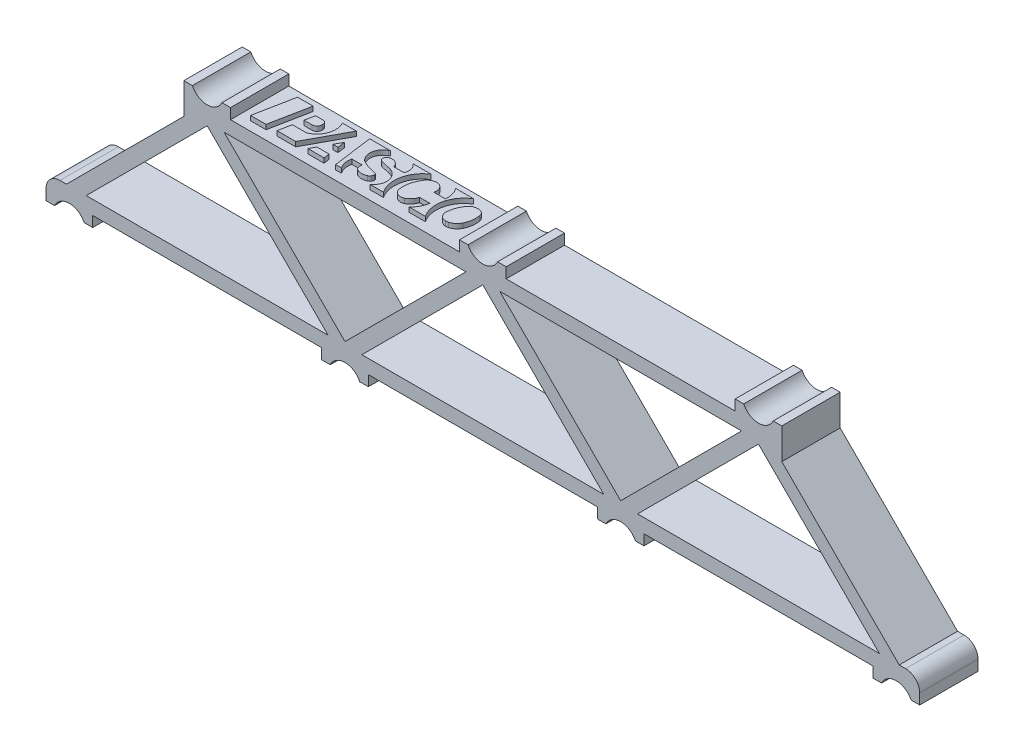
SolidWorks part; units mm, degrees
ref_plane "Front XY" through (0, 0, 0) normal (0, 0, 1) x (1, 0, 0)
ref_plane "Top XZ" through (0, 0, 0) normal (0, 1, 0) x (1, 0, 0)
ref_plane "Right YZ" through (0, 0, 0) normal (1, 0, 0) x (0, 0, -1)
sketch "Sketch1" plane through (0, 0, 0) normal (0, 0, 1) x (1, 0, 0)
  line L0 (-45, -15) -> (-15, -15) construction
  line L1 (-15, -15) -> (15, -15) construction
  line L2 (15, -15) -> (45, -15) construction
  line L3 (-45, -15) -> (-30, 0) construction
  line L4 (-30, 0) -> (-15, -15) construction
  line L5 (-15, -15) -> (0, 0) construction
  line L6 (0, 0) -> (15, -15) construction
  line L7 (15, -15) -> (30, 0) construction
  line L8 (30, 0) -> (45, -15) construction
  line L9 (-30, 0) -> (0, 0) construction
  line L10 (0, 0) -> (30, 0) construction
  line L11 (-43.1604, -14.238) -> (-30, -1.0776)
  line L12 (-30, -1.0776) -> (-16.8396, -14.238)
  line L13 (-43.1604, -14.238) -> (-16.8396, -14.238)
  line L14 (-28.1604, -0.762) -> (-15, -13.9224)
  line L15 (-15, -13.9224) -> (-1.8396, -0.762)
  line L16 (-28.1604, -0.762) -> (-1.8396, -0.762)
  line L17 (-13.1604, -14.238) -> (0, -1.0776)
  line L18 (0, -1.0776) -> (13.1604, -14.238)
  line L19 (-13.1604, -14.238) -> (13.1604, -14.238)
  line L20 (1.8396, -0.762) -> (15, -13.9224)
  line L21 (15, -13.9224) -> (28.1604, -0.762)
  line L22 (1.8396, -0.762) -> (28.1604, -0.762)
  line L23 (16.8396, -14.238) -> (30, -1.0776)
  line L24 (30, -1.0776) -> (43.1604, -14.238)
  line L25 (16.8396, -14.238) -> (43.1604, -14.238)
  line L26 (-46.8396, -15.762) -> (-30.3156, 0.762)
  line L27 (-30.3156, 0.762) -> (0, 0.762)
  line L28 (0, 0.762) -> (30.3156, 0.762)
  line L29 (30.3156, 0.762) -> (46.8396, -15.762)
  line L30 (15, -15.762) -> (46.8396, -15.762)
  line L31 (-15, -15.762) -> (15, -15.762)
  line L32 (-46.8396, -15.762) -> (-15, -15.762)
  dimension "D1" = 45
  dimension "D2" = 30
extrude "Boss-Extrude1" add sketch "Sketch1" along normal mid plane 6.35
sketch "Sketch2" plane through (0, 0, 0) normal (0, 0, 1) x (1, 0, 0)
  line L0 (-45, -15) -> (-45, -17.667) construction
  line L1 (-46.8396, -15.762) -> (-15, -15.762) construction
  line L2 (-46.6064, -16.905) -> (-47.54, -16.905)
  line L3 (-47.54, -16.905) -> (-47.54, -14.238)
  line L4 (-43.3936, -16.905) -> (-42.46, -16.905)
  line L5 (-42.46, -16.905) -> (-42.46, -14.238)
  line L6 (-42.46, -14.238) -> (-47.54, -14.238)
  line L7 (-27.46, 0.762) -> (-30.3156, 0.762)
  line L8 (-15, -15) -> (-15, -17.667) construction
  line L9 (-16.6064, -16.905) -> (-17.54, -16.905)
  line L10 (-17.54, -16.905) -> (-17.54, -15.762)
  line L11 (-13.3936, -16.905) -> (-12.46, -16.905)
  line L12 (-12.46, -16.905) -> (-12.46, -15.762)
  line L13 (-12.46, -15.762) -> (-17.54, -15.762)
  line L14 (-30.3156, 0.762) -> (0, 0.762) construction
  line L15 (-30, 0) -> (-30, 2.667) construction
  line L16 (-27.46, 0.762) -> (-27.46, 1.905)
  line L17 (-27.46, 1.905) -> (-28.3936, 1.905)
  line L18 (-32.54, 0.762) -> (-32.54, 1.905)
  line L19 (-32.54, 1.905) -> (-31.6064, 1.905)
  line L20 (-30.3156, 0.762) -> (-32.54, -1.4624)
  line L21 (-46.8396, -15.762) -> (-30.3156, 0.762) construction
  line L22 (-32.54, -1.4624) -> (-32.54, 0.762)
  line L23 (-46.8396, -15.762) -> (46.8396, -15.762) construction
  line L24 (-43.1604, -14.238) -> (-16.8396, -14.238) construction
  arc A0 (-43.3936, -16.905) -> (-46.6064, -16.905) centre (-45, -17.667) ccw
  arc A1 (-13.3936, -16.905) -> (-16.6064, -16.905) centre (-15, -17.667) ccw
  arc A2 (-31.6064, 1.905) -> (-28.3936, 1.905) centre (-30, 2.667) ccw
  dimension "D1" = 1.778
  dimension "D4" = 1.778
  dimension "D9" = 5.08
  dimension "D2" = 1.905
  dimension "D3" = 1.143
  dimension "D5" = 5.08
  dimension "D6" = 1.143
  dimension "D7" = 5.08
  dimension "D8" = 1.143
extrude "Boss-Extrude2" add sketch "Sketch2" against normal up to surface (3.175 mm away) and the other way up to surface (3.175 mm away) up to face at (15, -5.1488, -3.175) other way up to face at (15, -5.1488, 3.175)
sketch "Sketch3" plane through (0, 0, 0) normal (0, 0, 1) x (1, 0, 0)
  line L0 (0, 0) -> (0, 2.667) construction
  line L1 (1.6064, 1.905) -> (2.54, 1.905)
  line L2 (2.54, 1.905) -> (2.54, 0.762)
  line L3 (0, 0.762) -> (30.3156, 0.762) construction
  line L4 (2.54, 0.762) -> (-2.54, 0.762)
  line L5 (-30.3156, 0.762) -> (0, 0.762) construction
  line L6 (-2.54, 1.905) -> (-2.54, 0.762)
  line L7 (-1.6064, 1.905) -> (-2.54, 1.905)
  line L9 (-12.46, -15.762) -> (-17.54, -15.762) construction
  line L10 (-45, -15) -> (-45, -17.667) construction
  arc A0 (-1.6064, 1.905) -> (1.6064, 1.905) centre (0, 2.667) ccw
  arc A1 (-43.3936, -16.905) -> (-46.6064, -16.905) centre (-45, -17.667) ccw construction
  dimension "D1" = 1.143
extrude "Boss-Extrude3" add sketch "Sketch3" against normal up to surface and the other way up to surface
fillet "Fillet1" radius 1.524 1 edges at (-47.54, -14.238, 0)
mirror "Mirror1" about plane through (0, 0, 0) normal (1, 0, 0) of "Fillet1", "Boss-Extrude2"
sketch "Sketch4" plane through (30.3415, 0.762, -10.9983) normal (0, 1, 0) x (-1, 0, 0)
  line L0 (55.7666, 8.903) -> (54.0822, 8.903)
  line L1 (54.0822, 8.903) -> (54.9244, 13.1845)
  line L2 (56.6089, 13.1845) -> (55.7666, 8.903)
  line L3 (54.9244, 13.1845) -> (56.6089, 13.1845)
  line L4 (49.3737, 8.903) -> (51.6958, 13.1845)
  line L5 (53.7312, 13.1845) -> (53.4551, 11.7807)
  line L6 (47.3442, 13.1845) -> (47.9247, 8.903)
  line L7 (52.3626, 10.7279) -> (53.248, 10.7279)
  line L8 (53.248, 10.7279) -> (53.0409, 9.6751)
  line L9 (53.0409, 9.6751) -> (52.2241, 9.6751)
  line L10 (51.8362, 10.0631) -> (51.8362, 10.2015)
  line L11 (50.8536, 8.9732) -> (50.8886, 8.903)
  line L12 (50.8886, 8.903) -> (49.3737, 8.903)
  line L13 (53.4551, 11.7807) -> (52.0448, 11.7807)
  line L14 (48.9585, 10.5963) -> (48.8455, 11.4298)
  line L15 (48.8455, 11.4298) -> (49.4106, 11.4298)
  line L16 (49.4106, 11.4298) -> (48.9585, 10.5963)
  line L17 (45.6575, 8.903) -> (45.8001, 8.9732)
  line L18 (45.8829, 12.0583) -> (45.8829, 11.7807)
  line L19 (45.8829, 11.7807) -> (46.9933, 11.7807)
  line L20 (47.9247, 8.903) -> (45.6575, 8.903)
  line L21 (51.6958, 13.1845) -> (53.7312, 13.1845)
  line L22 (48.6076, 13.1845) -> (50.3622, 13.1845)
  line L23 (46.7125, 13.1845) -> (47.3442, 13.1845)
  line L24 (50.0196, 12.5528) -> (48.6932, 12.5528)
  line L25 (50.3622, 13.1845) -> (50.0196, 12.5528)
  line L26 (48.6932, 12.5528) -> (48.6076, 13.1845)
  line L27 (43.0934, 9.0079) -> (43.2038, 8.8974)
  line L28 (43.2038, 8.8974) -> (41.2386, 8.8974)
  line L29 (44.0085, 10.6319) -> (45.1372, 10.3497)
  line L30 (43.9769, 10.232) -> (42.8539, 10.232)
  line L31 (38.5708, 8.903) -> (36.6056, 8.903)
  line L32 (38.5708, 11.7105) -> (39.6938, 11.7105)
  line L33 (39.4131, 10.4472) -> (38.1497, 10.4472)
  line L34 (42.1504, 13.1845) -> (43.6243, 13.1845)
  line L35 (37.5882, 13.1845) -> (39.3429, 13.1845)
  line L36 (35.481, 9.6026) -> (35.3569, 9.6026)
  arc A0 (46.0025, 11.3297) -> (44.4424, 11.8336) centre (43.5988, 6.5555) ccw
  arc A1 (45.5669, 12.5268) -> (44.5843, 12.5069) centre (45.0989, 11.369) ccw
  arc A2 (45.3751, 9.9924) -> (45.1372, 10.3497) centre (45.0598, 10.0403) ccw
  arc A3 (45.0793, 9.6312) -> (45.3751, 9.9924) centre (44.9228, 10.0611) ccw
  arc A4 (45.8829, 12.0583) -> (45.5669, 12.5268) centre (45.3775, 12.0583) ccw
  arc A5 (46.9933, 11.7807) -> (46.7125, 13.1845) centre (45.2737, 12.1667) ccw
  arc A6 (51.8362, 10.0631) -> (52.2241, 9.6751) centre (52.2241, 10.0631) ccw
  arc A7 (52.3626, 10.7279) -> (51.8362, 10.2015) centre (52.3626, 10.2015) ccw
  arc A8 (52.0448, 11.7807) -> (51.7548, 11.7109) centre (52.0448, 11.1429) ccw
  arc A9 (51.7548, 11.7109) -> (50.8536, 8.9732) centre (52.6862, 9.8871) ccw
  arc A10 (45.8001, 8.9732) -> (46.1639, 11.2138) centre (45.1852, 10.2229) ccw
  arc A11 (46.1639, 11.2138) -> (46.0025, 11.3297) centre (45.7157, 10.76) ccw
  arc A12 (35.481, 9.6026) -> (36.2948, 10.0199) centre (35.481, 10.6046) ccw
  arc A13 (36.8641, 11.666) -> (36.0777, 12.512) centre (36.0532, 11.7008) ccw
  arc A14 (44.3262, 12.272) -> (44.2646, 12.0208) centre (44.6418, 12.0615) ccw
  arc A15 (41.2386, 8.8974) -> (42.1504, 13.1845) centre (39.5781, 11.491) ccw
  arc A16 (43.6243, 13.1845) -> (43.6095, 10.8085) centre (44.3995, 11.9916) ccw
  arc A17 (36.6056, 8.903) -> (37.5882, 13.1845) centre (35.0592, 11.5114) ccw
  arc A18 (39.3429, 13.1845) -> (38.5708, 11.7105) centre (41.058, 11.3469) ccw
  arc A19 (40.4153, 12.6039) -> (39.6938, 11.7105) centre (41.058, 11.3469) ccw
  arc A20 (41.5918, 11.9736) -> (40.4153, 12.6039) centre (40.7812, 11.8738) ccw
  arc A21 (44.2646, 12.0208) -> (44.4424, 11.8336) centre (44.476, 12.0436) ccw
  arc A22 (43.6095, 10.8085) -> (44.0085, 10.6319) centre (44.3179, 11.8694) ccw
  arc A23 (43.9769, 10.232) -> (45.0793, 9.6312) centre (44.793, 10.4176) ccw
  arc A24 (42.8539, 10.232) -> (43.0934, 9.0079) centre (43.8833, 9.7978) ccw
  arc A25 (41.1552, 9.9997) -> (41.5918, 11.9736) centre (38.5855, 11.6033) ccw
  arc A26 (40.2511, 9.3719) -> (41.1552, 9.9997) centre (40.1216, 10.5232) ccw
  arc A27 (39.4131, 10.4472) -> (40.2511, 9.3719) centre (40.1617, 10.1664) ccw
  arc A28 (38.1497, 10.4472) -> (38.5708, 8.903) centre (40.1617, 10.1664) ccw
  arc A29 (36.2948, 10.0199) -> (36.8641, 11.666) centre (33.8223, 11.7965) ccw
  arc A30 (44.5843, 12.5069) -> (44.3262, 12.272) centre (44.8175, 11.9913) ccw
  arc A31 (35.7478, 12.4758) -> (34.9205, 11.7781) centre (36.1351, 11.1771) ccw
  arc A32 (34.6919, 10.1578) -> (35.3569, 9.6026) centre (35.3569, 10.2783) ccw
  arc A33 (34.9205, 11.7781) -> (34.6919, 10.1578) centre (37.2562, 10.6225) ccw
  arc A34 (36.0777, 12.512) -> (35.7478, 12.4758) centre (36.0417, 11.3183) ccw
extrude "Boss-Extrude4" add sketch "Sketch4" along normal blind 0.508
